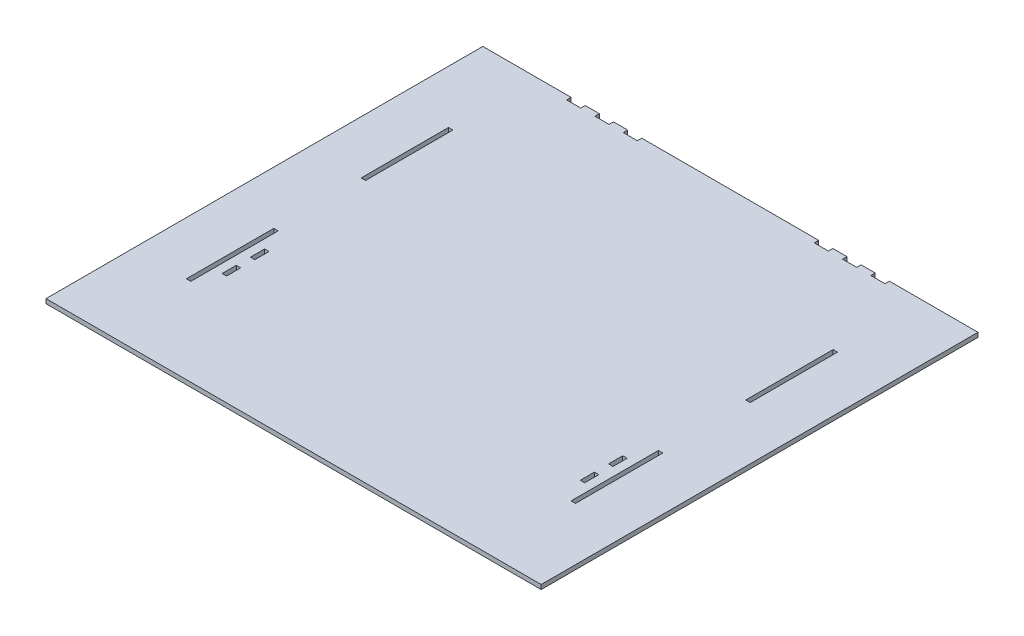
SolidWorks part; units mm, degrees
ref_plane "Front Plane" through (0, 0, 0) normal (0, 0, 1) x (1, 0, 0)
ref_plane "Top Plane" through (0, 0, 0) normal (0, 1, 0) x (1, 0, 0)
ref_plane "Right Plane" through (0, 0, 0) normal (1, 0, 0) x (0, 0, -1)
sketch "Sketch1" plane through (0, 0, 0) normal (0, 1, 0) x (1, 0, 0)
  line L0 (-215, -49.4) -> (-215, -148.2)
  line L1 (-280, 247) -> (-180.2136, 247)
  line L2 (-280, 247) -> (-280, -247)
  line L3 (-280, -247) -> (280, -247)
  line L4 (280, 247) -> (280, -247)
  line L5 (-280, 247) -> (280, -247) construction
  line L6 (-280, -247) -> (280, 247) construction
  line L7 (215, -49.4) -> (215, -148.2)
  line L8 (-200, -74.801) -> (-200, -90.8019)
  line L9 (215, 148.2) -> (215, 49.4)
  line L10 (-220, 148.2) -> (-220, 49.4)
  line L11 (-100.2136, 247) -> (99.7864, 247)
  line L12 (-100.2136, 242) -> (-116.2136, 242)
  line L13 (-220, -49.4) -> (-220, -148.2)
  line L14 (-180.2136, 242) -> (-180.2136, 247)
  line L15 (-220, 148.2) -> (-215, 148.2)
  line L16 (-220, 49.4) -> (-215, 49.4)
  line L17 (-220, -49.4) -> (-215, -49.4)
  line L18 (-220, -148.2) -> (-215, -148.2)
  line L19 (220, 148.2) -> (220, 49.4)
  line L20 (-100.2136, 242) -> (-100.2136, 247)
  line L21 (-132.2136, 242) -> (-148.2136, 242)
  line L22 (220, -49.4) -> (220, -148.2)
  line L23 (-132.2136, 247) -> (-116.2136, 247)
  line L24 (220, 148.2) -> (215, 148.2)
  line L25 (220, 49.4) -> (215, 49.4)
  line L26 (220, -49.4) -> (215, -49.4)
  line L27 (220, -148.2) -> (215, -148.2)
  line L28 (-215, 148.2) -> (-215, 49.4)
  line L29 (-164.2136, 242) -> (-180.2136, 242)
  line L30 (-164.2136, 242) -> (-164.2136, 247)
  line L31 (-148.2136, 242) -> (-148.2136, 247)
  line L32 (-132.2136, 242) -> (-132.2136, 247)
  line L33 (-116.2136, 242) -> (-116.2136, 247)
  line L34 (-164.2136, 247) -> (-148.2136, 247)
  line L35 (179.7864, 242) -> (179.7864, 247)
  line L36 (163.7864, 242) -> (179.7864, 242)
  line L37 (163.7864, 242) -> (163.7864, 247)
  line L39 (147.7864, 242) -> (147.7864, 247)
  line L40 (131.7864, 242) -> (147.7864, 242)
  line L41 (131.7864, 242) -> (131.7864, 247)
  line L43 (115.7864, 242) -> (115.7864, 247)
  line L44 (99.7864, 242) -> (115.7864, 242)
  line L45 (99.7864, 242) -> (99.7864, 247)
  line L46 (115.7864, 247) -> (131.7864, 247)
  line L47 (147.7864, 247) -> (163.7864, 247)
  line L48 (179.7864, 247) -> (280, 247)
  line L59 (205, -122.8038) -> (205, -106.8029)
  line L62 (205, -90.8019) -> (205, -74.801)
  line L65 (-205, -90.8019) -> (-205, -74.801)
  line L67 (-205, -122.8038) -> (-205, -106.8029)
  line L68 (-200, -106.8029) -> (-200, -122.8038)
  line L70 (200, -74.801) -> (200, -90.8019)
  line L72 (200, -106.8029) -> (200, -122.8038)
  line L74 (-200, -74.801) -> (-205, -74.801)
  line L75 (-200, -90.8019) -> (-205, -90.8019)
  line L76 (-200, -106.8029) -> (-205, -106.8029)
  line L77 (-200, -122.8038) -> (-205, -122.8038)
  line L78 (200, -74.801) -> (205, -74.801)
  line L79 (200, -90.8019) -> (205, -90.8019)
  line L80 (200, -106.8029) -> (205, -106.8029)
  line L81 (200, -122.8038) -> (205, -122.8038)
  point P0 (0, 0)
  dimension "D1" = 560
  dimension "D2" = 494
  dimension "D3" = 5
  dimension "D4" = 80
  dimension "D5" = 5
  dimension "D6" = 5
  dimension "D7" = 5
  dimension "D8" = 5
extrude "Boss-Extrude1" add sketch "Sketch1" along normal blind 5
